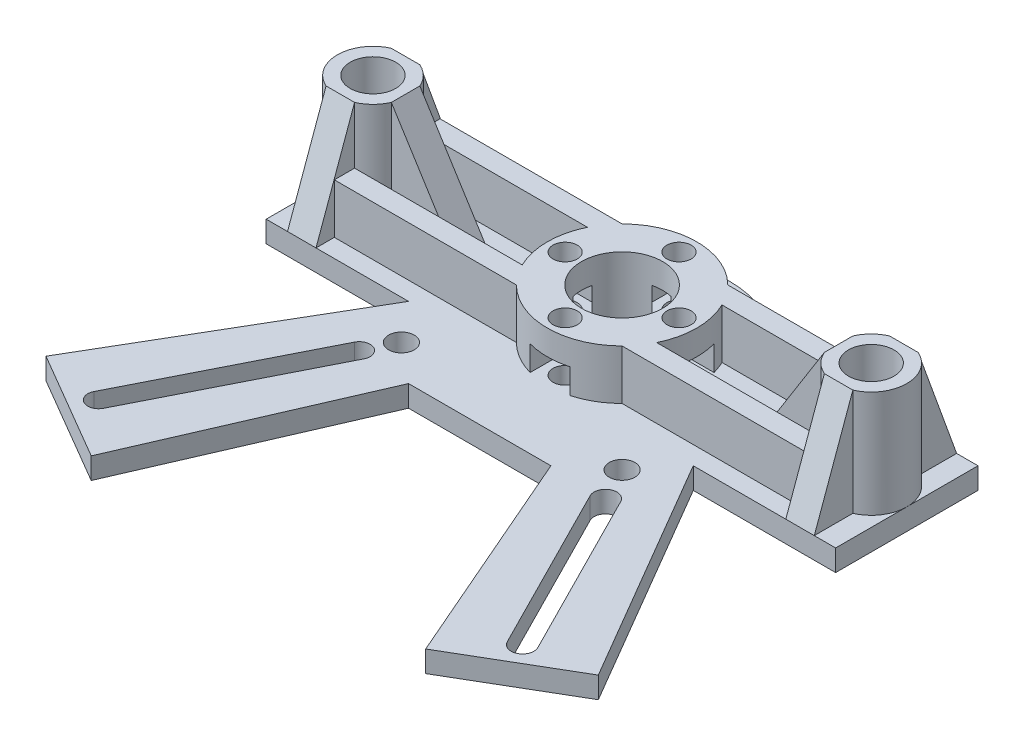
SolidWorks part; units mm, degrees
ref_plane "前视基准面" through (0, 0, 0) normal (0, 0, 1) x (1, 0, 0)
ref_plane "上视基准面" through (0, 0, 0) normal (0, 1, 0) x (1, 0, 0)
ref_plane "右视基准面" through (0, 0, 0) normal (1, 0, 0) x (0, 0, -1)
sketch "草图1" plane through (0, 0, 0) normal (0, 1, 0) x (1, 0, 0)
  line L0 (-35.0818, -10) -> (-40, -10)
  line L1 (-40, -10) -> (-40, 10)
  line L2 (-40, 10) -> (-11.1803, 10)
  line L3 (-9.9994, -20.0003) -> (10.0006, -20.0003)
  line L4 (40, 10) -> (40, -10)
  line L5 (40, -10) -> (20, -10)
  line L6 (-20, -10) -> (-38.7957, -42.1354)
  line L7 (10.0006, -20.0003) -> (23.4932, -51.0857)
  line L8 (20, -10) -> (38.796, -42.135)
  line L9 (-15.5, -15.5) -> (-31.1994, -46.5784) construction
  line L10 (15.5, -15.5) -> (31.1994, -46.5783) construction
  line L11 (-38.7957, -42.1354) -> (-23.4932, -51.0857)
  line L12 (-17.4886, -19.4366) -> (-29.776, -43.7606) construction
  line L13 (-16.1319, -20.122) -> (-28.4192, -44.4459)
  line L14 (-18.8453, -18.7513) -> (-31.1327, -43.0752)
  line L15 (17.824, -20.1595) -> (29.776, -43.7606) construction
  line L16 (19.2514, -19.4366) -> (31.2034, -43.0377)
  line L17 (16.3966, -20.8823) -> (28.3486, -44.4834)
  line L18 (11.1803, 10) -> (40, 10)
  line L19 (-35.0818, -10) -> (-20, -10)
  line L20 (-9.9994, -20.0003) -> (-23.4932, -51.0857)
  line L22 (23.4932, -51.0857) -> (38.796, -42.135)
  circle A0 centre (35, 0) radius 3.2
  circle A2 centre (-15.5, -15.5) radius 1.8
  circle A3 centre (15.5, -15.5) radius 1.8
  circle A4 centre (-35, 0) radius 3.2
  arc A6 (-16.1319, -20.122) -> (-18.8453, -18.7513) centre (-17.4886, -19.4366) ccw
  arc A7 (-31.1327, -43.0752) -> (-28.4192, -44.4459) centre (-29.776, -43.7606) ccw
  circle A8 centre (0, 0) radius 5.7
  circle A9 centre (-8, 0) radius 1.7
  circle A10 centre (0, 8) radius 1.7
  circle A11 centre (8, 0) radius 1.7
  circle A12 centre (0, -8) radius 1.7
  arc A13 (19.2514, -19.4366) -> (16.3966, -20.8823) centre (17.824, -20.1595) ccw
  arc A14 (28.3486, -44.4834) -> (31.2034, -43.0377) centre (29.776, -43.7606) ccw
  arc A17 (11.1803, 10) -> (-11.1803, 10) centre (0, 0) ccw
  point P34 (-33.1606, -34.0237)
  point P38 (-23.6323, -31.5986)
  point P43 (23.8, -31.96)
extrude "凸台-拉伸1" add sketch "草图1" along normal blind 3
sketch "草图2" plane through (0, 3, 0) normal (0, 1, 0) x (1, 0, 0)
  circle A0 centre (0, 0) radius 10.5
extrude "凸台-拉伸2" add sketch "草图2" along normal blind 7
sketch "草图4" plane through (0, 3, 0) normal (0, -1, 0) x (1, 0, 0)
  circle A1 centre (0, -8) radius 1.7
  circle A2 centre (-8, 0) radius 1.7
  circle A3 centre (8, 0) radius 1.7
  circle A4 centre (0, 8) radius 1.7
extrude "切除-拉伸1" cut sketch "草图4" against normal blind 7
sketch "草图5" plane through (0, 3, 0) normal (0, 1, 0) x (1, 0, 0)
  line L1 (-4.7668, 0) -> (-6.3834, 2.8)
  line L2 (-6.3834, 2.8) -> (-11.2332, 2.8)
  line L5 (-11.2332, -2.8) -> (-6.3834, -2.8)
  line L6 (-6.3834, -2.8) -> (-4.7668, 0)
  line L7 (4.7668, 0) -> (6.3834, -2.8)
  line L8 (6.3834, -2.8) -> (11.2332, -2.8)
  line L11 (11.2332, 2.8) -> (6.3834, 2.8)
  line L12 (6.3834, 2.8) -> (4.7668, 0)
  line L14 (-2.8, 11.2332) -> (-2.8, 6.3834)
  line L15 (-2.8, 6.3834) -> (0, 4.7668)
  line L16 (0, 4.7668) -> (2.8, 6.3834)
  line L17 (2.8, 6.3834) -> (2.8, 11.2332)
  line L19 (0, -4.7668) -> (-2.8, -6.3834)
  line L20 (-2.8, -6.3834) -> (-2.8, -11.2332)
  line L23 (2.8, -11.2332) -> (2.8, -6.3834)
  line L24 (2.8, -6.3834) -> (0, -4.7668)
  line L25 (-11.2332, 2.8) -> (-11.2332, -2.8)
  line L29 (-2.8, 11.2332) -> (2.8, 11.2332)
  line L32 (11.2332, 2.8) -> (11.2332, -2.8)
  line L35 (-2.8, -11.2332) -> (2.8, -11.2332)
  line L39 (-1.4, -10.4249) -> (0, -11.2332) [skipped]
  line L40 (1.4, -10.4249) -> (2.8, -9.6166) [skipped]
  line L41 (9.6166, -2.8) -> (10.4249, -1.4) [skipped]
  line L42 (11.2332, 0) -> (10.4249, 1.4) [skipped]
  line L43 (1.4, 10.4249) -> (0, 11.2332) [skipped]
  line L44 (0, 11.2332) -> (-1.4, 10.4249) [skipped]
  line L45 (-10.4249, -1.4) -> (-9.6166, -2.8) [skipped]
  line L46 (-9.6166, 2.8) -> (-10.4249, 1.4) [skipped]
extrude "切除-拉伸2" cut sketch "草图5" along normal blind 3.5
sketch "草图6" plane through (0, 3, 0) normal (0, -1, 0) x (1, 0, 0)
  circle A0 centre (0, 0) radius 5.7
extrude "切除-拉伸3" cut sketch "草图6" against normal blind 20
sketch "草图7" plane through (0, 3, 0) normal (0, 1, 0) x (1, 0, 0)
  circle A0 centre (-35, 0) radius 3.2
  circle A1 centre (-35, 0) radius 5
  circle A2 centre (35, 0) radius 3.2
  circle A3 centre (35, 0) radius 5
extrude "凸台-拉伸3" add sketch "草图7" along normal blind 15
sketch "草图8" plane through (0, 3, 0) normal (0, 1, 0) x (1, 0, 0)
  line L0 (-11.1803, 10) -> (-40, 10) construction
  line L1 (-31, -2) -> (-21, -2)
  line L2 (-31, -2) -> (-31, 2)
  line L3 (-31, 2) -> (-21, 2)
  line L4 (-21, -2) -> (-21, 2)
  line L5 (-33, 4) -> (-37, 4)
  line L6 (-33, 4) -> (-33, 10)
  line L7 (-33, 10) -> (-37, 10)
  line L8 (-37, 4) -> (-37, 10)
  line L9 (-40, -10) -> (-20, -10) construction
  line L10 (-37, -4) -> (-33, -4)
  line L11 (-37, -4) -> (-37, -10)
  line L12 (-37, -10) -> (-33, -10)
  line L13 (-33, -4) -> (-33, -10)
  line L14 (40, 10) -> (11.1803, 10) construction
  line L15 (31, 2) -> (21, 2)
  line L16 (31, 2) -> (31, -2)
  line L17 (31, -2) -> (21, -2)
  line L18 (21, 2) -> (21, -2)
  line L19 (33, 4) -> (37, 4)
  line L20 (33, 4) -> (33, 10)
  line L21 (33, 10) -> (37, 10)
  line L22 (37, 4) -> (37, 10)
  line L23 (20, -10) -> (40, -10) construction
  line L24 (33, -4) -> (37, -4)
  line L25 (33, -4) -> (33, -10)
  line L26 (33, -10) -> (37, -10)
  line L27 (37, -4) -> (37, -10)
extrude "凸台-拉伸4" add sketch "草图8" along normal blind 15
sketch "草图9" plane through (0, 0, 2) normal (0, 0, 1) x (1, 0, 0)
  line L0 (-30.4174, 18) -> (-21, 3)
  line L1 (-30.4174, 18) -> (-21, 18)
  line L2 (-30.4174, 18) -> (-21, 18) construction
  line L3 (-21, 18) -> (-21, 3)
  line L4 (21, 3) -> (30.4174, 18)
  line L5 (30.4174, 18) -> (21, 18)
  line L6 (21, 18) -> (21, 3)
extrude "切除-拉伸4" cut sketch "草图9" against normal blind 15
sketch "草图10" plane through (33, 0, 0) normal (-1, 0, 0) x (0, 0, 1)
  line L0 (-4.5826, 18) -> (-10, 3)
  line L1 (-10, 18) -> (-10, 3) construction
  line L2 (-10, 3) -> (-10, 18)
  line L3 (-10, 18) -> (-4.5826, 18) construction
  line L4 (-10, 18) -> (-4.5826, 18)
  line L5 (4.5826, 18) -> (10, 18)
  line L6 (10, 18) -> (10, 3)
  line L7 (4.5826, 3) -> (10, 3) construction
  line L8 (10, 18) -> (10, 3) construction
  line L9 (10, 3) -> (4.5826, 18)
extrude "切除-拉伸5" cut sketch "草图10" against normal blind 15
sketch "草图11" plane through (-33, 0, 0) normal (1, 0, 0) x (0, 0, -1)
  line L0 (-4.5826, 18) -> (-10, 3)
  line L1 (-10, 3) -> (-10, 18)
  line L2 (-10, 18) -> (-4.5826, 18)
  line L3 (4.5826, 18) -> (10, 3)
  line L4 (10, 3) -> (10, 18)
  line L5 (10, 18) -> (4.5826, 18)
extrude "切除-拉伸6" cut sketch "草图11" against normal blind 15
sketch "草图12" plane through (0, 3, 0) normal (0, 1, 0) x (1, 0, 0)
  line L1 (-33, -4.5826) -> (-7.4246, -4.5826)
  line L2 (-33, -4.5826) -> (-33, -7.4246)
  line L3 (-33, -7.4246) -> (-7.4246, -7.4246)
  line L4 (-7.4246, -4.5826) -> (-7.4246, -7.4246)
  line L5 (-33, 4.5826) -> (-7.4246, 4.5826)
  line L6 (-33, 4.5826) -> (-33, 7.4246)
  line L7 (-33, 7.4246) -> (-7.4246, 7.4246)
  line L8 (-7.4246, 4.5826) -> (-7.4246, 7.4246)
  line L9 (33, 4.5826) -> (7.4246, 4.5826)
  line L10 (33, 4.5826) -> (33, 7.4246)
  line L11 (33, 7.4246) -> (7.4246, 7.4246)
  line L12 (7.4246, 4.5826) -> (7.4246, 7.4246)
  line L13 (33, -4.5826) -> (7.4246, -4.5826)
  line L14 (33, -4.5826) -> (33, -7.4246)
  line L15 (33, -7.4246) -> (7.4246, -7.4246)
  line L16 (7.4246, -4.5826) -> (7.4246, -7.4246)
  arc A0 (-10.1198, -2.8) -> (-2.8, -10.1198) centre (0, 0) ccw construction
  arc A1 (-2.8, 10.1198) -> (-10.1198, 2.8) centre (0, 0) ccw construction
  arc A2 (10.1198, 2.8) -> (2.8, 10.1198) centre (0, 0) ccw construction
  arc A3 (2.8, -10.1198) -> (10.1198, -2.8) centre (0, 0) ccw construction
extrude "凸台-拉伸5" add sketch "草图12" along normal blind 7
